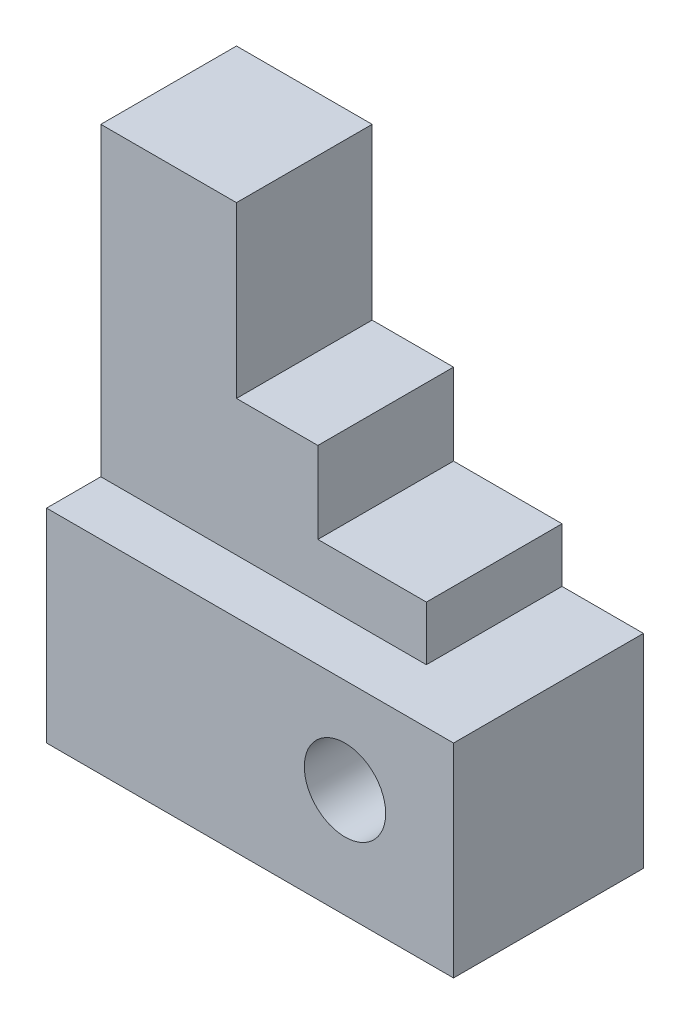
SolidWorks part; units mm, degrees
ref_plane "Front Plane" through (0, 0, 0) normal (0, 0, 1) x (1, 0, 0)
ref_plane "Top Plane" through (0, 0, 0) normal (0, 1, 0) x (1, 0, 0)
ref_plane "Right Plane" through (0, 0, 0) normal (1, 0, 0) x (0, 0, -1)
sketch "Sketch1" plane through (0, 0, 0) normal (0, 0, 1) x (1, 0, 0)
  line L1 (30, -15) -> (-30, -15)
  line L2 (30, -15) -> (30, 15)
  line L3 (30, 15) -> (-30, 15)
  line L4 (-30, -15) -> (-30, 15)
  line L5 (30, -15) -> (-30, 15) construction
  line L6 (30, 15) -> (-30, -15) construction
  circle A0 centre (14, 1) radius 6
  point P0 (0, 0)
  point P8 (30, 0)
  dimension "D3" = 12
  dimension "D1" = 30
  dimension "D2" = 60
  dimension "D4" = 16
  dimension "D5" = 16
extrude "Boss-Extrude1" add sketch "Sketch1" along normal blind 28 contours L4 L1 L2 L3 A0
sketch "Sketch2" plane through (0, 0, 0) normal (0, 0, -1) x (-1, 0, 0)
  line L0 (-30, -15) -> (-30, 15) construction
  line L1 (30, 15) -> (-18, 15)
  line L2 (30, 15) -> (30, 23)
  line L3 (30, 23) -> (-18, 23)
  line L4 (-18, 15) -> (-18, 23)
  line L5 (30, 15) -> (-18, 23) construction
  line L6 (30, 23) -> (-18, 15) construction
  line L7 (-30, -15) -> (30, -15) construction
  line L8 (30, 23) -> (-2, 23)
  line L9 (30, 23) -> (30, 35)
  line L10 (30, 35) -> (-2, 35)
  line L11 (-2, 23) -> (-2, 35)
  line L12 (30, 23) -> (-2, 35) construction
  line L13 (30, 35) -> (-2, 23) construction
  line L14 (30, 35) -> (10, 35)
  line L15 (30, 35) -> (30, 60)
  line L16 (30, 60) -> (10, 60)
  line L17 (10, 35) -> (10, 60)
  line L18 (30, 35) -> (10, 60) construction
  line L19 (30, 60) -> (10, 35) construction
  point P4 (6, 19)
  point P11 (14, 29)
  point P15 (20, 47.5)
  line M11 (30, 15) -> (-30, 15)
  dimension "D1" = 12
  dimension "D2" = 12
  dimension "D3" = 20
  dimension "D4" = 75
  dimension "D5" = 20
  dimension "D6" = 12
extrude "Boss-Extrude2" add sketch "Sketch2" against normal blind 20 contours L4 L2 L3 M11 | L11 L3 L9 L10 | L17 L10 L15 L16
